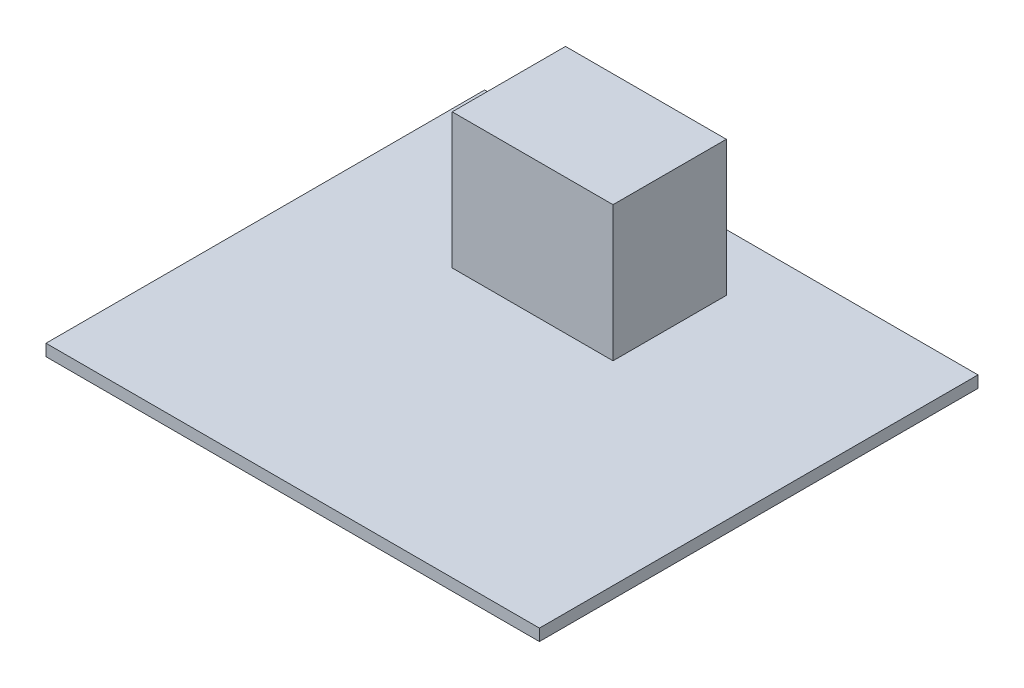
SolidWorks part; units mm, degrees
ref_plane "Front Plane" through (0, 0, 0) normal (0, 0, 1) x (1, 0, 0)
ref_plane "Top Plane" through (0, 0, 0) normal (0, 1, 0) x (1, 0, 0)
ref_plane "Right Plane" through (0, 0, 0) normal (1, 0, 0) x (0, 0, -1)
sketch "Sketch1" plane through (0, 0, 0) normal (0, 1, 0) x (1, 0, 0)
  line L1 (-33.75, 30) -> (33.75, 30)
  line L2 (-33.75, 30) -> (-33.75, -30)
  line L3 (-33.75, -30) -> (33.75, -30)
  line L4 (33.75, 30) -> (33.75, -30)
  line L5 (-33.75, 30) -> (33.75, -30) construction
  line L6 (-33.75, -30) -> (33.75, 30) construction
  point P0 (0, 0)
  dimension "D1" = 67.5
  dimension "D2" = 60
extrude "Boss-Extrude1" add sketch "Sketch1" along normal blind 1.6
sketch "Sketch2" plane through (0, 1.6, 0) normal (0, 1, 0) x (1, 0, 0)
  line L1 (-14.88, 22.2) -> (7.12, 22.2)
  line L2 (-14.88, 22.2) -> (-14.88, 6.7)
  line L3 (-14.88, 6.7) -> (7.12, 6.7)
  line L4 (7.12, 22.2) -> (7.12, 6.7)
  line L5 (-14.88, 22.2) -> (7.12, 6.7) construction
  line L6 (-14.88, 6.7) -> (7.12, 22.2) construction
  line L7 (33.75, 30) -> (-33.75, 30) construction
  line L8 (-33.75, 30) -> (-33.75, -30) construction
  point P0 (-3.88, 14.45)
  point P6 (-11, 7.75)
  point P7 (-5.204, 11.9566)
  dimension "D1" = 15.5
  dimension "D2" = 22
  dimension "D3" = 7.8
  dimension "D4" = 18.87
extrude "Boss-Extrude2" add sketch "Sketch2" along normal blind 18.5
